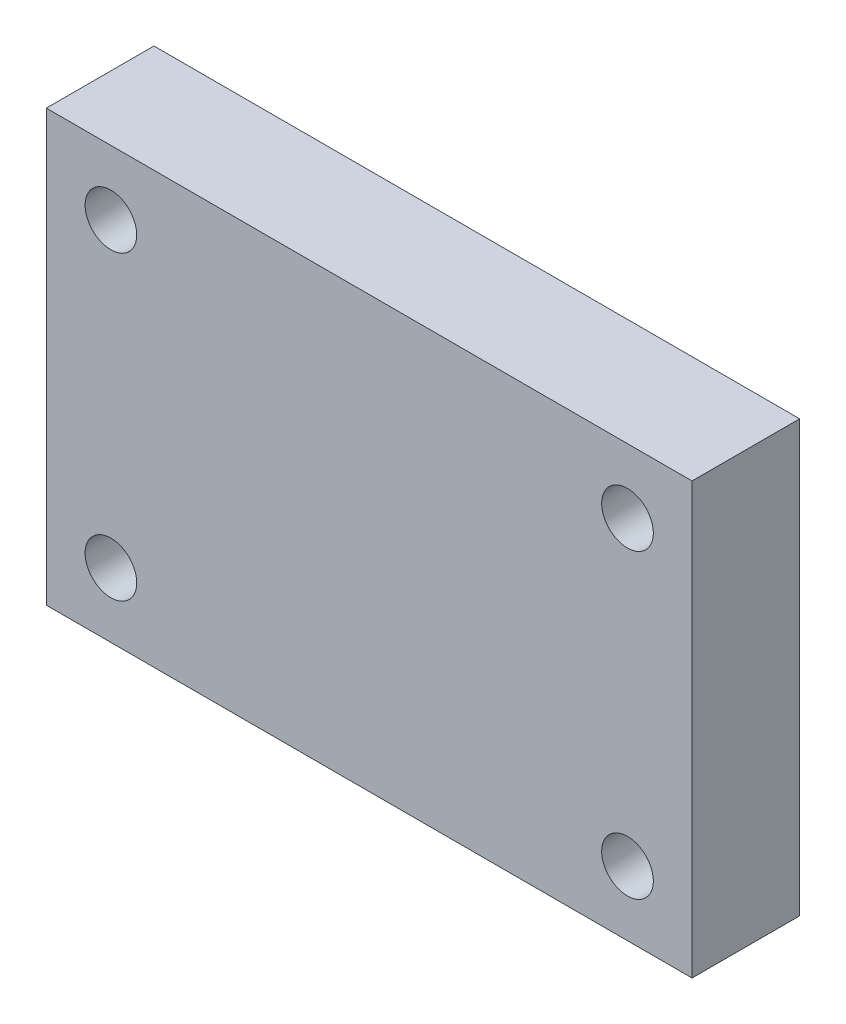
SolidWorks part; units mm, degrees
ref_plane "Front Plane" through (0, 0, 0) normal (0, 0, 1) x (1, 0, 0)
ref_plane "Top Plane" through (0, 0, 0) normal (0, 1, 0) x (1, 0, 0)
ref_plane "Right Plane" through (0, 0, 0) normal (1, 0, 0) x (0, 0, -1)
sketch "Sketch1" plane through (0, 0, 0) normal (0, 0, 1) x (1, 0, 0)
  line L0 (0, -12.7) -> (0, 17.5441) construction
  line L1 (-19.05, -12.7) -> (19.05, -12.7)
  line L2 (-19.05, -12.7) -> (-19.05, 12.7)
  line L3 (-19.05, 12.7) -> (19.05, 12.7)
  line L4 (19.05, -12.7) -> (19.05, 12.7)
  line L5 (-19.05, -12.7) -> (19.05, 12.7) construction
  line L6 (-19.05, 12.7) -> (19.05, -12.7) construction
  line L7 (0, 0) -> (-19.05, 0) construction
  line L8 (-15.24, -12.7) -> (-15.24, 12.7) construction
  line L9 (15.24, -12.7) -> (15.24, 12.7) construction
  circle A0 centre (-15.24, 8.89) radius 1.524
  circle A1 centre (-15.24, -8.89) radius 1.524
  circle A2 centre (15.24, 8.89) radius 1.524
  circle A3 centre (15.24, -8.89) radius 1.524
  point P0 (0, 0)
  dimension "D3" = 3.81
  dimension "D5" = 3.81
  dimension "D6" = 3.048
  dimension "D1" = 25.4
  dimension "D2" = 38.1
  dimension "D4" = 3.81
extrude "Boss-Extrude1" add sketch "Sketch1" along normal blind 6.35
